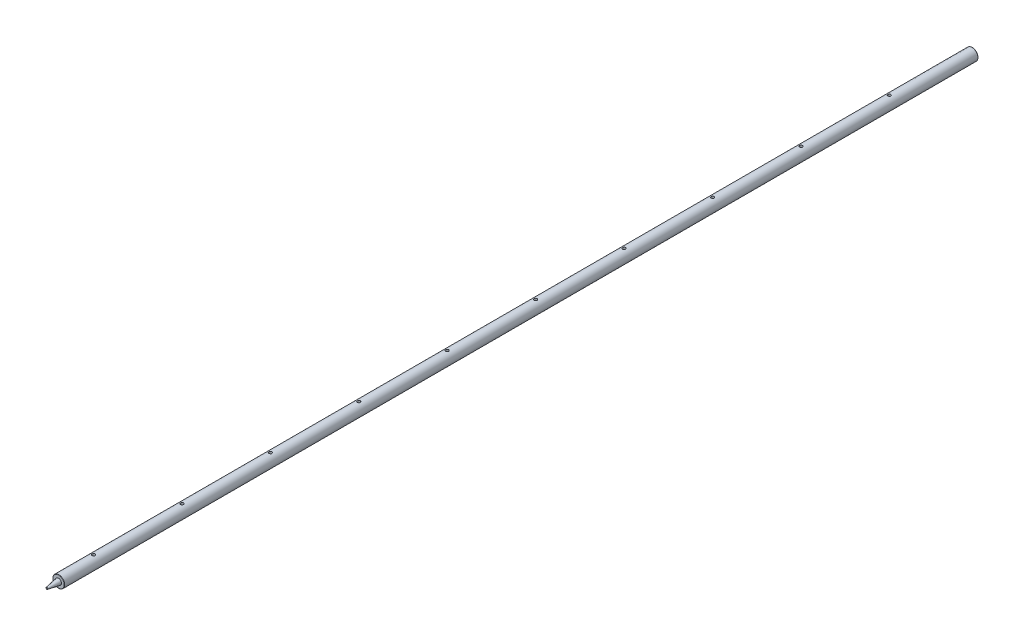
SolidWorks part; units mm, degrees
material "6061-T6 (SS)"
ref_plane "Front Plane" through (0, 0, 0) normal (0, 0, 1) x (1, 0, 0)
ref_plane "Top Plane" through (0, 0, 0) normal (0, 1, 0) x (1, 0, 0)
ref_plane "Right Plane" through (0, 0, 0) normal (1, 0, 0) x (0, 0, -1)
sketch "Sketch1" plane through (0, 0, 0) normal (0, 1, 0) x (1, 0, 0)
  line L0 (0, 1550) -> (0, -20)
  line L1 (0, -20) -> (1.4735, -20)
  line L2 (1.4735, -20) -> (5, 0)
  line L3 (5, 0) -> (10, 0)
  line L4 (0, 1550) -> (10, 1550)
  line L7 (0, 1550) -> (0, 78.6298) construction
  line L9 (10, 0) -> (10, 1550)
  dimension "D2" = 1550
  dimension "D5" = 20
  dimension "D8" = 20
  dimension "D9" = 10
  dimension "D10" = 100
revolve "Revolve1" add sketch "Sketch1" angle 360 about L7
fillet "Fillet1" radius 0.508 3 edges at (-10, 0, 0) (-1.4735, 0, 20) (-10, 0, -1550)
sketch "Sketch2" plane through (0, 0, 0) normal (0, 1, 0) x (1, 0, 0)
  line L0 (0, 652.025) -> (0, 1109.225) construction
  dimension "D1" = 652.025
  dimension "D2" = 457.2
sketch "Sketch4" plane through (0, 0, 0) normal (1, 0, 0) x (0, 0, -1)
  line L0 (1109.225, 0) -> (1109.225, 56.1053) construction
  line L1 (652.025, 0) -> (1109.225, 0) construction
  line L2 (652.025, 0) -> (652.025, 76.4057) construction
hole_wizard "M6x1.0 Tapped Hole1" positions "3DSketch1" profile "Sketch3" tap size "M6x1.0" standard "Ansi Metric"
sketch3d "3DSketch1"
  line L1 (0, 0, -1109.225) -> (0, 56.1053, -1109.225) construction
  point P1 (0, 10, -1109.225)
sketch "Sketch3" plane through (0, 10, -1109.225) normal (1, 0, 0) x (0, 0, 1)
  line L0 (0, 0) -> (0, 16.5022)
  line L1 (0, 16.5022) -> (2.5, 15)
  line L2 (2.5, 15) -> (2.5, 0)
  line L5 (2.5, 0) -> (0, 0)
  line L10 (0, 16.5022) -> (-2.5, 15) construction
  line L11 (0, -6.35) -> (0, 107.95) construction
  dimension "Tap Drill Dia." = 5
  dimension "Tap Drill Depth" = 15
  dimension "Drill Angle" = 118
cosmetic thread "Hole Thread1" parameters "D1"=12, "D2"=6
pattern_linear "LPattern1" count 8 spacing 150 along (0, 0, 1) count 3 spacing 150 along (0, 0, -1) of "M6x1.0 Tapped Hole1"
